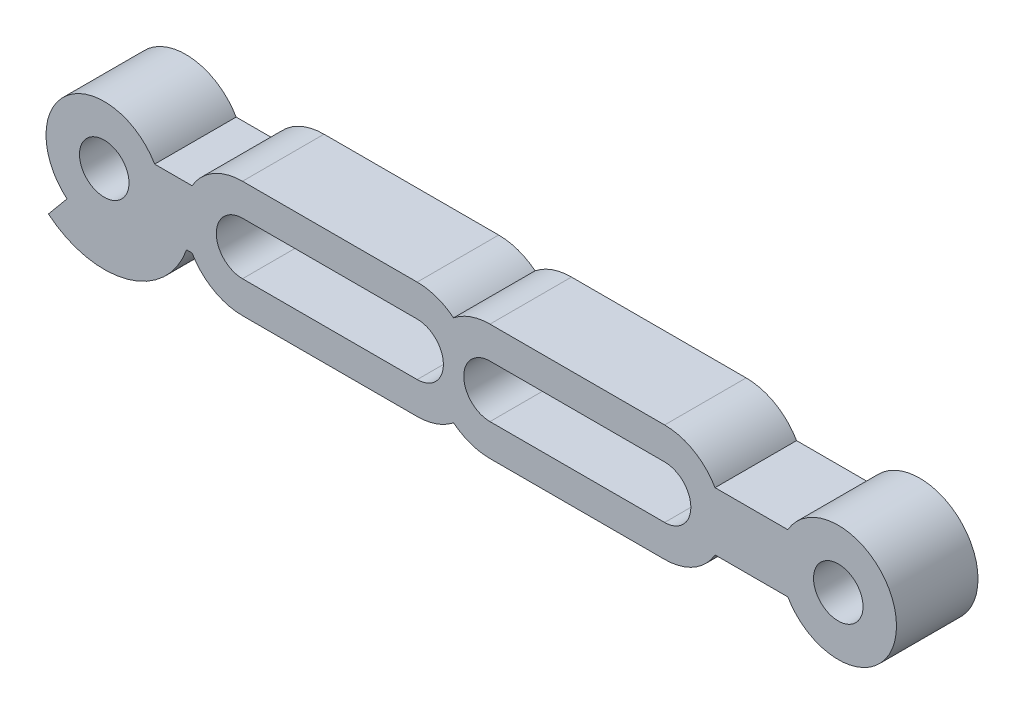
SolidWorks part; units mm, degrees
ref_plane "Спереди" through (0, 0, 0) normal (0, 0, 1) x (1, 0, 0)
ref_plane "Сверху" through (0, 0, 0) normal (0, 1, 0) x (1, 0, 0)
ref_plane "Справа" through (0, 0, 0) normal (1, 0, 0) x (0, 0, -1)
other "Configuration Table"
sketch "Эскиз1" plane through (0, 0, 0) normal (0, 0, 1) x (1, 0, 0)
  line L0 (0, 1.8) -> (12, 1.8)
  line L1 (0, -1.8) -> (12, -1.8)
  line L2 (17, 1.8) -> (29, 1.8)
  line L3 (17, -1.8) -> (29, -1.8)
  line L4 (-64.4883, 0) -> (100.5473, 0) construction
  line L5 (0, 4) -> (12, 4)
  line L7 (0, -4) -> (12, -4)
  line L13 (-12.056, -3.0769) -> (-13.3339, -4.6153)
  line L14 (-3.8431, 2) -> (-6.0359, 2)
  line L19 (17, -4) -> (29, -4)
  line L20 (17, 4) -> (29, 4)
  line L22 (-3.8431, 2) -> (-3.4641, 2)
  line L24 (-3.8431, -2) -> (-3.4641, -2)
  line L26 (32.4641, 2) -> (37.4641, 2)
  line L28 (32.4641, -2) -> (37.4641, -2)
  arc A0 (0, 1.8) -> (0, -1.8) centre (0, 0) ccw
  arc A1 (12, -1.8) -> (12, 1.8) centre (12, 0) ccw
  arc A2 (17, 1.8) -> (17, -1.8) centre (17, 0) ccw
  arc A3 (29, -1.8) -> (29, 1.8) centre (29, 0) ccw
  arc A5 (14.5, 3.1225) -> (12, 4) centre (12, 0) ccw
  arc A6 (14.5, -3.1225) -> (17, -4) centre (17, 0) ccw
  arc A8 (12, -4) -> (14.5, -3.1225) centre (12, 0) ccw
  arc A9 (-3.4641, -2) -> (0, -4) centre (0, 0) ccw
  arc A10 (0, 4) -> (-3.4641, 2) centre (0, 0) ccw
  arc A11 (17, 4) -> (14.5, 3.1225) centre (17, 0) ccw
  arc A12 (29, -4) -> (32.4641, -2) centre (29, 0) ccw
  arc A13 (32.4641, 2) -> (29, 4) centre (29, 0) ccw
  circle A14 centre (40.9282, 0) radius 1.7
  arc A15 (37.4641, -2) -> (37.4641, 2) centre (40.9282, 0) ccw
  circle A16 centre (-9.5, 0) radius 1.7
  arc A18 (-6.0359, 2) -> (-13.3987, 0.8946) centre (-9.5, 0) ccw
  arc A19 (-13.3987, 0.8946) -> (-12.056, -3.0769) centre (-9.5, 0) ccw
  arc A20 (-13.3339, -4.6153) -> (-3.8431, -2) centre (-9.5, 0) ccw
  point P1 (6, 1.8)
  point P4 (23, 1.8)
  point P6 (6, -1.8)
  dimension "D3" = 3.6
  dimension "D4" = 8
  dimension "D10" = 4
  dimension "D11" = 8
  dimension "D12" = 8
  dimension "D13" = 6
  dimension "D19" = 3.4
  dimension "D20" = 8
  dimension "D21" = 3.4
  dimension "D22" = 3.0769
  dimension "D9" = 4
  dimension "D5" = 12
  dimension "D6" = 12
  dimension "D7" = 17
  dimension "D8" = 3.6
  dimension "D15" = 4
  dimension "D16" = 4
  dimension "D17" = 9.5
  dimension "D18" = 5
  dimension "D23" = 0.8946
extrude "Бобышка-Вытянуть1" add sketch "Эскиз1" along normal blind 5.6
